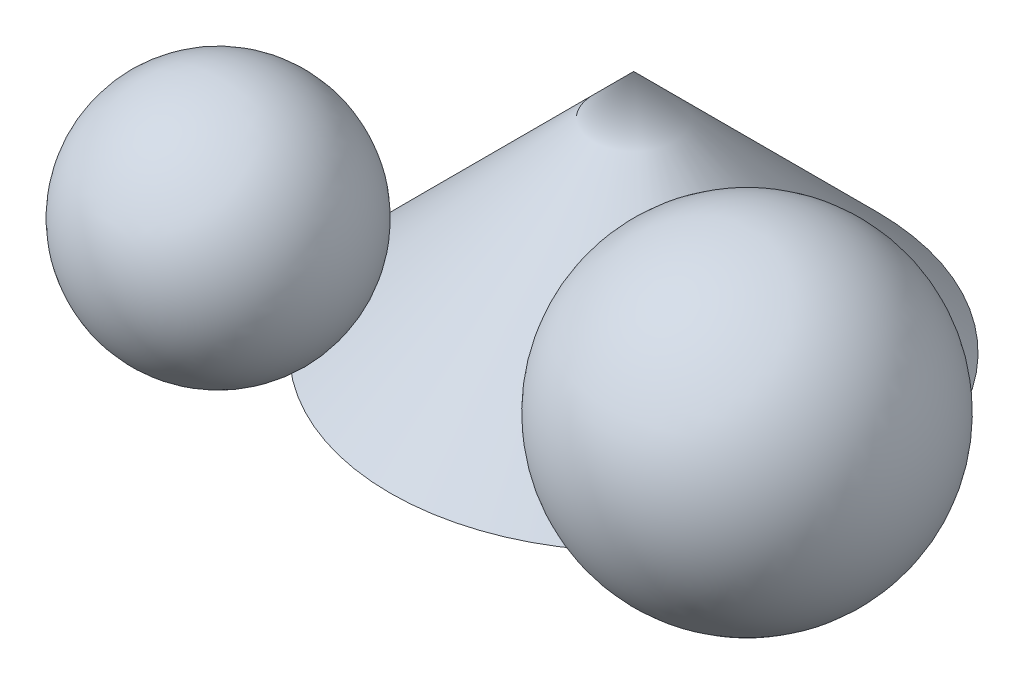
SolidWorks part; units mm, degrees
ref_plane "Front" through (0, 0, 0) normal (0, 0, 1) x (1, 0, 0)
ref_plane "Top" through (0, 0, 0) normal (0, 1, 0) x (1, 0, 0)
ref_plane "Right" through (0, 0, 0) normal (1, 0, 0) x (0, 0, -1)
sketch "Sketch1" plane through (0, 0, 0) normal (0, 1, 0) x (1, 0, 0)
  circle A0 centre (0, 0) radius 40
  dimension "D1" = 80
sketch "Sketch2" plane through (0, 0, 0) normal (0, 0, 1) x (1, 0, 0)
  point P0 (0, 40)
  dimension "D1" = 40
loft "Loft1" add profiles "Sketch2", "Sketch1"
ref_plane "Plane1" through (0, 20, 0) normal (0, 1, 0) x (-1, 0, 0)
sketch "Sketch4" plane through (0, 0, 0) normal (0, 0, 1) x (1, 0, 0)
  line L0 (0, 40) -> (-40, 0) construction
  line L1 (-40, 0) -> (40, 0) construction
  circle A0 centre (-48.2843, 20) radius 20
  dimension "D1" = 40
sketch "Sketch5" plane through (0, 20, 0) normal (0, 1, 0) x (-1, 0, 0)
  line L0 (-4.863, 35) -> (71.81, 35) construction
  line L1 (33.2622, 55) -> (33.2622, 15)
  circle A0 centre (0, 0) radius 48.2843 construction
  arc A1 (33.2622, 15) -> (33.2622, 55) centre (33.2622, 35) ccw
  dimension "D2" = 40
  dimension "D1" = 35
revolve "Revolve1" add sketch "Sketch5" angle 360 about L1
sketch "Sketch6" plane through (0, 0, 0) normal (0, 1, 0) x (1, 0, 0)
  line L0 (0, 0) -> (47.9814, 0) construction
  line L1 (0, 0) -> (41.0804, -23.7178) construction
  line L2 (28, 8.6038) -> (28, -34.0283) construction
  point P6 (28, -16.1658)
  dimension "D1" = 28
  dimension "D2" = 30
ref_plane "Plane2" through (0, 0, 0) normal (-0.5, 0, 0.866) x (0.866, 0, 0.5)
sketch "Sketch8" plane through (0, 0, 0) normal (-0.5, 0, 0.866) x (0.866, 0, 0.5)
  line L0 (32.3316, 0) -> (32.3316, 7.6684) construction
  line L1 (0, 40) -> (40, 0) construction
  line L4 (0, 0) -> (41.5531, 0) construction
  line L5 (50.8447, 52.363) -> (50.8447, 0)
  arc A0 (50.8447, 52.363) -> (50.8447, 0) centre (50.8447, 26.1815) ccw
revolve "Revolve2" add sketch "Sketch8" angle 360 about L5
